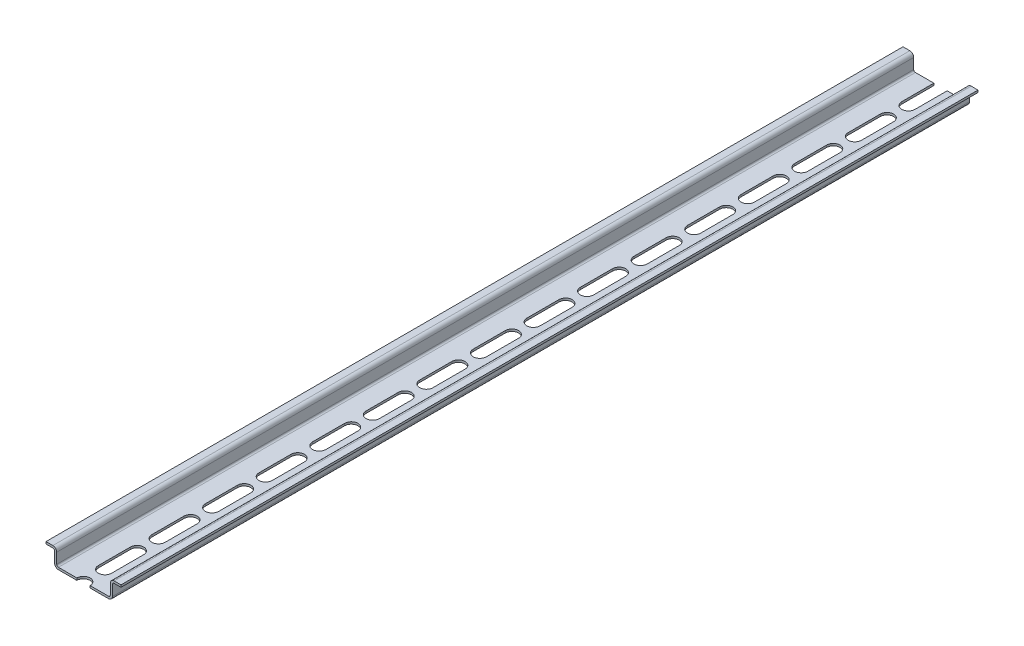
SolidWorks part; units mm, degrees
ref_plane "Front Plane" through (0, 0, 0) normal (0, 0, 1) x (1, 0, 0)
ref_plane "Top Plane" through (0, 0, 0) normal (0, 1, 0) x (1, 0, 0)
ref_plane "Right Plane" through (0, 0, 0) normal (1, 0, 0) x (0, 0, -1)
sketch "Sketch1" plane through (0, 0, 0) normal (0, 0, 1) x (1, 0, 0)
  line L0 (0, 0) -> (-11.7, 0)
  line L5 (-13.5, 1.8) -> (-13.5, 6.7)
  line L6 (-14.3, 7.5) -> (-17.5, 7.5)
  line L15 (0, 0) -> (0, 12.268) construction
  line L16 (0, 1) -> (-11.7, 1)
  line L17 (-12.5, 1.8) -> (-12.5, 6.7)
  line L18 (-14.3, 8.5) -> (-17.5, 8.5)
  line L19 (-17.5, 8.5) -> (-17.5, 7.5)
  line L20 (17.5, 8.5) -> (17.5, 7.5)
  line L21 (14.3, 8.5) -> (17.5, 8.5)
  line L22 (12.5, 1.8) -> (12.5, 6.7)
  line L23 (0, 1) -> (11.7, 1)
  line L24 (14.3, 7.5) -> (17.5, 7.5)
  line L25 (13.5, 1.8) -> (13.5, 6.7)
  line L26 (0, 0) -> (11.7, 0)
  arc A0 (-11.7, 0) -> (-13.5, 1.8) centre (-11.7, 1.8) cw
  arc A1 (-13.5, 6.7) -> (-14.3, 7.5) centre (-14.3, 6.7) ccw
  arc A2 (-11.7, 1) -> (-12.5, 1.8) centre (-11.7, 1.8) cw
  arc A3 (-12.5, 6.7) -> (-14.3, 8.5) centre (-14.3, 6.7) ccw
  arc A4 (12.5, 6.7) -> (14.3, 8.5) centre (14.3, 6.7) cw
  arc A5 (11.7, 1) -> (12.5, 1.8) centre (11.7, 1.8) ccw
  arc A6 (13.5, 6.7) -> (14.3, 7.5) centre (14.3, 6.7) cw
  arc A7 (11.7, 0) -> (13.5, 1.8) centre (11.7, 1.8) ccw
  point P0 (0, 0)
  point P6 (-13.5, 0)
  point P10 (-13.5, 7.5)
  point P16 (13.5, 7.5)
  point P31 (13.5, 0)
  dimension "D4" = 1.8
  dimension "D6" = 0.8
  dimension "D7" = 1.8
  dimension "D8" = 8.5
  dimension "D1" = 17.5
  dimension "D2" = 7.5
  dimension "D3" = 11.7
  dimension "D5" = 1
  dimension "D9" = 35
  dimension "D10" = 27
extrude "Boss-Extrude2" add sketch "Sketch1" along normal blind 400
sketch "Sketch2" plane through (0, 1, 0) normal (0, 1, 0) x (1, 0, 0)
  line L0 (0, -390) -> (0, -375) construction
  line L1 (-3.1, -390) -> (-3.1, -375)
  line L2 (3.1, -390) -> (3.1, -375)
  line L3 (0, -365) -> (0, -350) construction
  line L6 (-3.1, -365) -> (-3.1, -350)
  line L7 (3.1, -365) -> (3.1, -350)
  line L8 (11.7, 0) -> (-11.7, 0) construction
  line L9 (11.7, -400) -> (-11.7, -400) construction
  line L10 (0, -340) -> (0, -325) construction
  line L11 (-3.1, -340) -> (-3.1, -325)
  line L12 (3.1, -340) -> (3.1, -325)
  line L13 (0, -315) -> (0, -300) construction
  line L14 (-3.1, -315) -> (-3.1, -300)
  line L15 (3.1, -315) -> (3.1, -300)
  line L16 (0, -415) -> (0, -400) construction
  line L17 (-3.1, -415) -> (-3.1, -400)
  line L18 (3.1, -415) -> (3.1, -400)
  line L19 (0, -290) -> (0, -275) construction
  line L22 (-3.1, -290) -> (-3.1, -275)
  line L25 (3.1, -290) -> (3.1, -275)
  line L28 (0, -265) -> (0, -250) construction
  line L31 (-3.1, -265) -> (-3.1, -250)
  line L34 (3.1, -265) -> (3.1, -250)
  line L35 (0, -240) -> (0, -225) construction
  line L36 (-3.1, -240) -> (-3.1, -225)
  line L37 (3.1, -240) -> (3.1, -225)
  line L38 (0, -215) -> (0, -200) construction
  line L39 (-3.1, -215) -> (-3.1, -200)
  line L40 (3.1, -215) -> (3.1, -200)
  line L41 (0, -190) -> (0, -175) construction
  line L42 (-3.1, -190) -> (-3.1, -175)
  line L43 (3.1, -190) -> (3.1, -175)
  line L44 (0, -165) -> (0, -150) construction
  line L45 (-3.1, -165) -> (-3.1, -150)
  line L46 (3.1, -165) -> (3.1, -150)
  line L47 (0, -140) -> (0, -125) construction
  line L48 (-3.1, -140) -> (-3.1, -125)
  line L49 (3.1, -140) -> (3.1, -125)
  line L50 (0, -115) -> (0, -100) construction
  line L51 (-3.1, -115) -> (-3.1, -100)
  line L52 (3.1, -115) -> (3.1, -100)
  line L53 (0, -90) -> (0, -75) construction
  line L54 (-3.1, -90) -> (-3.1, -75)
  line L55 (3.1, -90) -> (3.1, -75)
  line L56 (0, -65) -> (0, -50) construction
  line L57 (-3.1, -65) -> (-3.1, -50)
  line L58 (3.1, -65) -> (3.1, -50)
  line L59 (0, -40) -> (0, -25) construction
  line L60 (-3.1, -40) -> (-3.1, -25)
  line L61 (3.1, -40) -> (3.1, -25)
  line L62 (0, -15) -> (0, 0) construction
  line L63 (-3.1, -15) -> (-3.1, 0)
  line L64 (3.1, -15) -> (3.1, 0)
  arc A0 (-3.1, -390) -> (3.1, -390) centre (0, -390) ccw
  arc A1 (3.1, -375) -> (-3.1, -375) centre (0, -375) ccw
  arc A4 (-3.1, -365) -> (3.1, -365) centre (0, -365) ccw
  arc A5 (3.1, -350) -> (-3.1, -350) centre (0, -350) ccw
  arc A6 (-3.1, -340) -> (3.1, -340) centre (0, -340) ccw
  arc A7 (3.1, -325) -> (-3.1, -325) centre (0, -325) ccw
  arc A8 (-3.1, -315) -> (3.1, -315) centre (0, -315) ccw
  arc A9 (3.1, -300) -> (-3.1, -300) centre (0, -300) ccw
  arc A10 (-3.1, -415) -> (3.1, -415) centre (0, -415) ccw
  arc A11 (3.1, -400) -> (-3.1, -400) centre (0, -400) ccw
  arc A22 (-3.1, -290) -> (3.1, -290) centre (0, -290) ccw
  arc A23 (3.1, -275) -> (-3.1, -275) centre (0, -275) ccw
  arc A24 (-3.1, -265) -> (3.1, -265) centre (0, -265) ccw
  arc A25 (3.1, -250) -> (-3.1, -250) centre (0, -250) ccw
  arc A26 (-3.1, -240) -> (3.1, -240) centre (0, -240) ccw
  arc A27 (3.1, -225) -> (-3.1, -225) centre (0, -225) ccw
  arc A28 (-3.1, -215) -> (3.1, -215) centre (0, -215) ccw
  arc A29 (3.1, -200) -> (-3.1, -200) centre (0, -200) ccw
  arc A30 (-3.1, -190) -> (3.1, -190) centre (0, -190) ccw
  arc A31 (3.1, -175) -> (-3.1, -175) centre (0, -175) ccw
  arc A32 (-3.1, -165) -> (3.1, -165) centre (0, -165) ccw
  arc A33 (3.1, -150) -> (-3.1, -150) centre (0, -150) ccw
  arc A34 (-3.1, -140) -> (3.1, -140) centre (0, -140) ccw
  arc A35 (3.1, -125) -> (-3.1, -125) centre (0, -125) ccw
  arc A36 (-3.1, -115) -> (3.1, -115) centre (0, -115) ccw
  arc A37 (3.1, -100) -> (-3.1, -100) centre (0, -100) ccw
  arc A38 (-3.1, -90) -> (3.1, -90) centre (0, -90) ccw
  arc A39 (3.1, -75) -> (-3.1, -75) centre (0, -75) ccw
  arc A40 (-3.1, -65) -> (3.1, -65) centre (0, -65) ccw
  arc A41 (3.1, -50) -> (-3.1, -50) centre (0, -50) ccw
  arc A42 (-3.1, -40) -> (3.1, -40) centre (0, -40) ccw
  arc A43 (3.1, -25) -> (-3.1, -25) centre (0, -25) ccw
  arc A44 (-3.1, -15) -> (3.1, -15) centre (0, -15) ccw
  arc A45 (3.1, 0) -> (-3.1, 0) centre (0, 0) ccw
  point P3 (0, -382.5)
  point P10 (0, -357.5)
  point P18 (0, 0)
  point P22 (0, -400)
  point P24 (0, -282.5)
  point P27 (0, -332.5)
  point P35 (0, -307.5)
  point P43 (0, -407.5)
  point P52 (0, -257.5)
  point P59 (0, -232.5)
  point P66 (0, -207.5)
  point P73 (0, -182.5)
  point P80 (0, -157.5)
  point P87 (0, -132.5)
  point P94 (0, -107.5)
  point P101 (0, -82.5)
  point P108 (0, -57.5)
  point P115 (0, -32.5)
  point P122 (0, -7.5)
  dimension "D1" = 15
  dimension "D2" = 6.2
  dimension "D5" = 25
  dimension "D6" = 10
  dimension "D8" = 25
  dimension "D11" = 25
  dimension "D14" = 25
  dimension "D3" = 15
  dimension "D4" = 6.2
  dimension "D7" = 15
  dimension "D9" = 6.2
  dimension "D10" = 15
  dimension "D12" = 6.2
  dimension "D13" = 15
  dimension "D15" = 6.2
  dimension "D16" = 2
  dimension "D17" = 25
  dimension "D18" = 4
  dimension "D19" = 5
  dimension "D20" = 5
extrude "Cut-Extrude1" cut sketch "Sketch2" against normal blind 100
